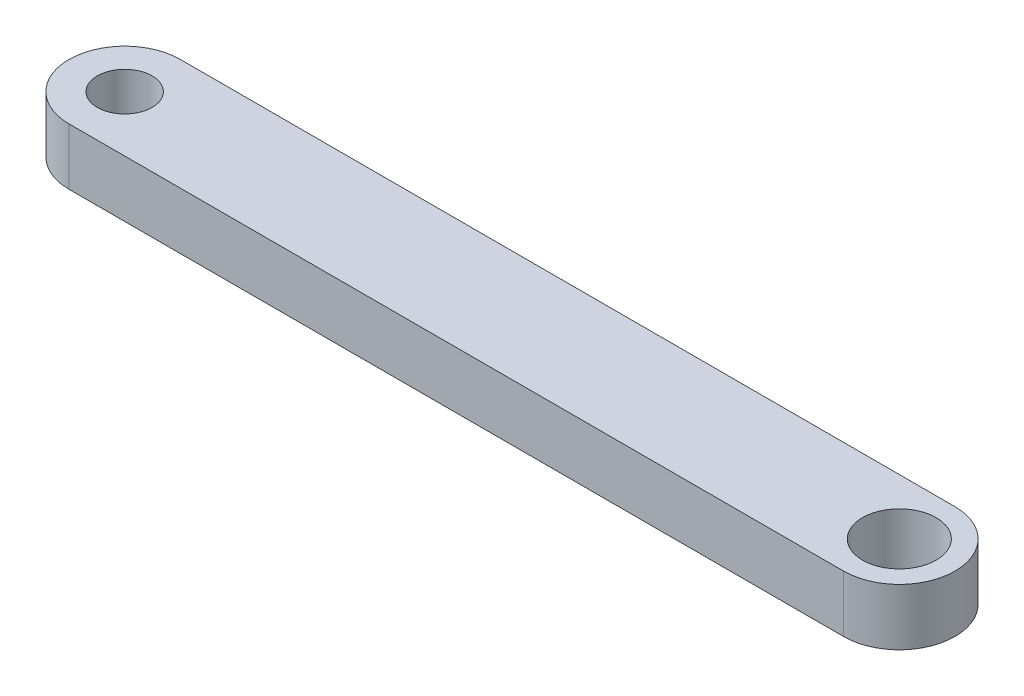
SolidWorks part; units mm, degrees
ref_plane "Front Plane" through (0, 0, 0) normal (0, 0, 1) x (1, 0, 0)
ref_plane "Top Plane" through (0, 0, 0) normal (0, 1, 0) x (1, 0, 0)
ref_plane "Right Plane" through (0, 0, 0) normal (1, 0, 0) x (0, 0, -1)
ref_plane "Plane1" through (0, 0, 0) normal (0, -1, 0) x (1, 0, 0)
sketch "Sketch1" plane through (0, 0, 0) normal (0, -1, 0) x (1, 0, 0)
  line L0 (32, 2.95) -> (-9, 2.95)
  line L1 (-9, -2.95) -> (32, -2.95)
  line L3 (32, 0) -> (31.9997, -0.0002) construction
  line L4 (32, 0) -> (32.0173, -0.0096) construction
  line L5 (32, 0) -> (32.0096, 0.0173) construction
  line L7 (32, 0) -> (32.0001, -0.0001) construction
  arc A0 (-9, 2.95) -> (-9, -2.95) centre (-9, 0) ccw
  arc A1 (32, -2.95) -> (32, 2.95) centre (32, 0) ccw
  circle A2 centre (32, 0) radius 1.95
  circle A3 centre (-9, 0) radius 1.45
  point P9 (-11.95, 0)
  point P10 (34.95, 0)
  point P22 (53.2116, 8.66)
  dimension "D1" = 2.9
  dimension "D2" = 3.9
  dimension "D3" = 2.95
  dimension "D4" = 41
  dimension "D5" = 9
extrude "Boss-Extrude1" add sketch "Sketch1" against normal blind 3
